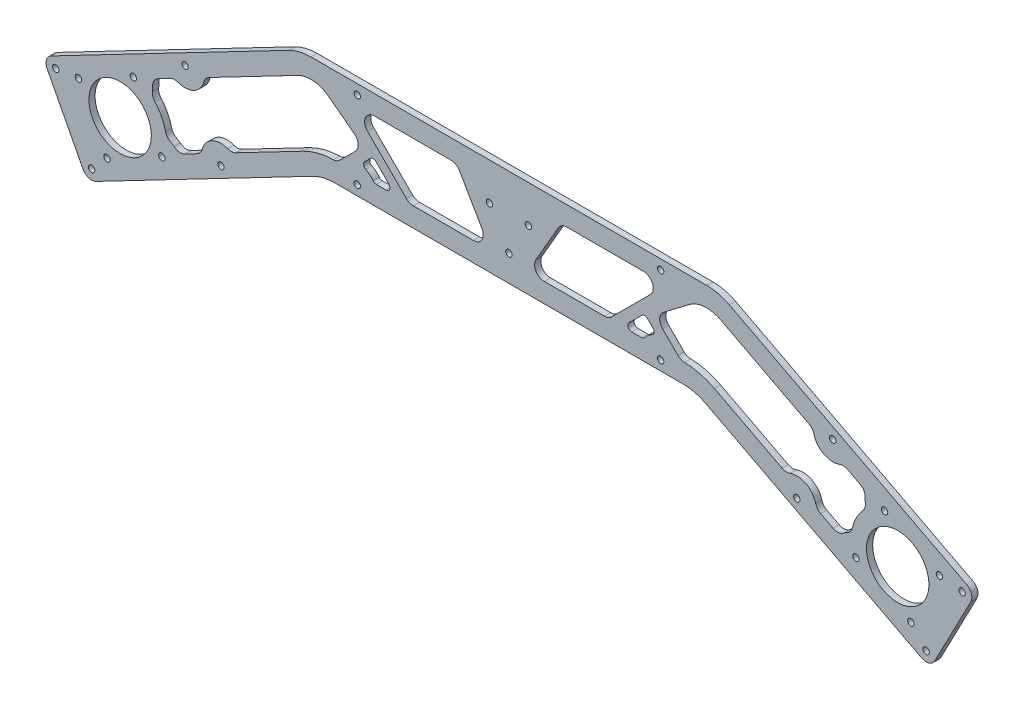
SolidWorks part; units mm, degrees
material "6061-T6 (SS)"
ref_plane "Front Plane" through (0, 0, 0) normal (0, 0, 1) x (1, 0, 0)
ref_plane "Top Plane" through (0, 0, 0) normal (0, 1, 0) x (1, 0, 0)
ref_plane "Right Plane" through (0, 0, 0) normal (1, 0, 0) x (0, 0, -1)
sketch "Sketch1" plane through (0, 0, 0) normal (0, 0, 1) x (1, 0, 0)
  line L0 (-200, -104.1134) -> (0, 0) construction
  line L1 (0, 0) -> (200, -104.1134) construction
  line L2 (-221.4586, -97.3475) -> (-193.2341, -82.6548) construction
  line L3 (-113.3558, -30.8247) -> (-235.4371, -94.3763)
  line L4 (-237.5634, -101.1201) -> (-219.0935, -136.6005)
  line L5 (-212.3497, -138.7268) -> (-101.1208, -80.8247)
  line L6 (-101.8121, -28) -> (101.8121, -28)
  line L7 (0, -28) -> (0, -78) construction
  line L8 (89.5771, -78) -> (-89.5771, -78)
  line L9 (113.3558, -30.8247) -> (235.4371, -94.3763)
  line L10 (237.5634, -101.1201) -> (219.0935, -136.6005)
  line L11 (212.3497, -138.7268) -> (101.1208, -80.8247)
  circle A1 centre (-200, -104.1134) radius 16.05
  circle A2 centre (-221.4586, -97.3475) radius 1.65
  circle A3 centre (-193.2341, -82.6548) radius 1.65
  circle A4 centre (-178.5414, -110.8793) radius 1.65
  circle A5 centre (-206.7659, -125.572) radius 1.65
  arc A6 (-235.4371, -94.3763) -> (-237.5634, -101.1201) centre (-233.1284, -98.8113) ccw
  arc A7 (-219.0935, -136.6005) -> (-212.3497, -138.7268) centre (-214.6584, -134.2918) ccw
  circle A8 centre (0, 0) radius 25 construction
  circle A11 centre (-200, -104.1134) radius 33.55 construction
  circle A12 centre (206.7659, -125.572) radius 1.65
  circle A13 centre (221.4586, -97.3475) radius 1.65
  circle A14 centre (193.2341, -82.6548) radius 1.65
  circle A15 centre (178.5414, -110.8793) radius 1.65
  circle A16 centre (200, -104.1134) radius 16.05
  arc A17 (235.4371, -94.3763) -> (237.5634, -101.1201) centre (233.1284, -98.8113) cw
  arc A18 (219.0935, -136.6005) -> (212.3497, -138.7268) centre (214.6584, -134.2918) cw
  circle A19 centre (-10, -47.2265) radius 1.65
  circle A20 centre (10, -47.2265) radius 1.65
  circle A21 centre (0, -64.547) radius 1.65
  arc A22 (101.1208, -80.8247) -> (89.5771, -78) centre (89.5771, -103) ccw
  arc A23 (113.3558, -30.8247) -> (101.8121, -28) centre (101.8121, -53) ccw
  arc A24 (-113.3558, -30.8247) -> (-101.8121, -28) centre (-101.8121, -53) cw
  arc A25 (-101.1208, -80.8247) -> (-89.5771, -78) centre (-89.5771, -103) cw
  point P17 (-200, -104.1134)
  point P27 (0, -53)
  point P28 (0, -25)
  point P53 (0, -53)
  point P54 (95.6946, -78)
  point P57 (107.9295, -28)
  point P60 (-107.9295, -28)
  point P63 (-95.6946, -78)
  dimension "D1" = 400
  dimension "D3" = 32.1
  dimension "D5" = 3.3
  dimension "D7" = 50
  dimension "D10" = 5
  dimension "D11" = 3.3
  dimension "D12" = 67.1
  dimension "D14" = 3
  dimension "D16" = 25
  dimension "D2" = 125
  dimension "D6" = 45
  dimension "D8" = 3
  dimension "D9" = 50
  dimension "D13" = 50
  dimension "D15" = 20
  dimension "D4" = 4
extrude "Base" add sketch "Sketch1" along normal blind 3.175
sketch "Sketch3" plane through (0, 0, 3.175) normal (0, 0, 1) x (1, 0, 0)
  line L1 (-89.5771, -78) -> (89.5771, -78) construction
  line L2 (-228.3285, -118.8603) -> (-185.7635, -96.7023) construction
  line L3 (101.8121, -28) -> (-101.8121, -28) construction
  line L4 (-237.5634, -101.1201) -> (-219.0935, -136.6005) construction
  line L5 (0, -28) -> (0, -78) construction
  circle A0 centre (-214.6584, -134.2918) radius 1.65
  circle A1 centre (-148.1326, -99.6606) radius 1.65
  circle A2 centre (-78.0312, -73) radius 1.65
  circle A3 centre (-78.0312, -33) radius 1.65
  circle A4 centre (-200, -104.1134) radius 16.05 construction
  circle A5 centre (-166.6026, -64.1802) radius 1.65
  circle A6 centre (-233.1284, -98.8113) radius 1.65
  circle A7 centre (233.1284, -98.8113) radius 1.65
  circle A8 centre (166.6026, -64.1802) radius 1.65
  circle A9 centre (78.0312, -33) radius 1.65
  circle A10 centre (78.0312, -73) radius 1.65
  circle A11 centre (148.1326, -99.6606) radius 1.65
  circle A12 centre (214.6584, -134.2918) radius 1.65
  dimension "D1" = 3.3
  dimension "D3" = 75
  dimension "D6" = 5
  dimension "D4" = 5
  dimension "D5" = 75
  dimension "D2" = 2
extrude "Strut Holes" cut sketch "Sketch3" against normal through all
sketch "Sketch4" plane through (0, 0, 0) normal (0, 0, -1) x (-1, 0, 0)
  line L0 (-166.7326, -103.7062) -> (-160.3585, -100.3881)
  line L1 (-101.1208, -80.8247) -> (-212.3497, -138.7268) construction
  line L2 (-140.5243, -90.063) -> (-105.7383, -71.9546)
  line L3 (-86.9223, -66.5452) -> (-79.0095, -58.6325)
  line L4 (-79.5169, -51.1182) -> (-92.7277, -41.0638)
  line L5 (-180.585, -77.0959) -> (-174.2109, -73.7777)
  line L6 (-235.4371, -94.3763) -> (-113.3558, -30.8247) construction
  line L7 (-154.3768, -63.4527) -> (-108.7383, -39.6948)
  line L8 (89.5771, -78) -> (-89.5771, -78) construction
  line L9 (-68.2844, -68) -> (-63.1994, -68)
  line L10 (-61.7852, -64.5858) -> (-68.4242, -57.9467)
  line L11 (-71.2527, -57.9467) -> (-74.1321, -60.8262)
  line L12 (-25.4306, -40.5) -> (-13.8835, -60.5)
  line L13 (-18.2137, -68) -> (-49.2288, -68)
  line L14 (-52.7643, -66.5355) -> (-72.7643, -46.5355)
  line L15 (-69.2288, -38) -> (-29.7607, -38)
  line L16 (-101.8121, -28) -> (101.8121, -28) construction
  line L17 (0, -28) -> (0, -78) construction
  line L18 (52.7643, -66.5355) -> (72.7643, -46.5355)
  line L19 (18.2137, -68) -> (49.2288, -68)
  line L20 (25.4306, -40.5) -> (13.8835, -60.5)
  line L21 (69.2288, -38) -> (29.7607, -38)
  line L22 (68.2844, -68) -> (63.1994, -68)
  line L23 (61.7852, -64.5858) -> (68.4242, -57.9467)
  line L24 (71.2527, -57.9467) -> (74.1321, -60.8262)
  line L25 (154.3768, -63.4527) -> (108.7383, -39.6948)
  line L26 (180.585, -77.0959) -> (174.2109, -73.7777)
  line L27 (166.7326, -103.7062) -> (160.3585, -100.3881)
  line L28 (140.5243, -90.063) -> (105.7383, -71.9546)
  line L29 (86.9223, -66.5452) -> (79.0095, -58.6325)
  line L30 (79.5169, -51.1182) -> (92.7277, -41.0638)
  arc A0 (-182.112, -88.1128) -> (-176.6329, -98.638) centre (-200, -104.1134) cw
  arc A1 (-174.0237, -101.958) -> (-172.208, -103.1405) centre (-178.5414, -110.8793) cw
  arc A2 (-183.3349, -84.0711) -> (-183.2622, -81.9056) centre (-193.2341, -82.6548) ccw
  arc A3 (-157.8223, -97.1889) -> (-144.5996, -90.3055) centre (-148.1326, -99.6606) cw
  arc A4 (-105.7383, -71.9546) -> (-90.3477, -68.0085) centre (-89.5771, -103) cw
  arc A5 (-89.5771, -78) -> (-101.1208, -80.8247) centre (-89.5771, -103) ccw construction
  arc A6 (-170.1356, -73.5353) -> (-156.9129, -66.6519) centre (-166.6026, -64.1802) ccw
  arc A7 (-108.7383, -39.6948) -> (-92.7277, -41.0638) centre (-101.8121, -53) cw
  arc A8 (-101.8121, -28) -> (-113.3558, -30.8247) centre (-101.8121, -53) ccw construction
  arc A9 (-69.9089, -67.1667) -> (-73.6035, -64.0337) centre (-78.0312, -73) ccw
  circle A10 centre (-10, -47.2265) radius 10 construction
  circle A11 centre (0, -64.547) radius 10 construction
  arc A12 (-156.9129, -66.6519) -> (-154.3768, -63.4527) centre (-152.068, -67.8878) cw
  arc A13 (-174.2109, -73.7777) -> (-170.1356, -73.5353) centre (-171.9022, -78.2128) cw
  arc A14 (-183.2622, -81.9056) -> (-180.585, -77.0959) centre (-178.2763, -81.5309) cw
  arc A15 (-182.112, -88.1128) -> (-183.3349, -84.0711) centre (-178.3853, -84.7793) cw
  arc A16 (-176.6329, -98.638) -> (-174.0237, -101.958) centre (-171.7648, -97.4973) ccw
  arc A17 (-172.208, -103.1405) -> (-166.7326, -103.7062) centre (-169.0413, -99.2712) ccw
  arc A18 (-160.3585, -100.3881) -> (-157.8223, -97.1889) centre (-162.6672, -95.953) ccw
  arc A19 (-144.5996, -90.3055) -> (-140.5243, -90.063) centre (-142.833, -85.628) ccw
  arc A20 (-79.0095, -58.6325) -> (-79.5169, -51.1182) centre (-82.545, -55.0969) ccw
  arc A21 (-90.3477, -68.0085) -> (-86.9223, -66.5452) centre (-90.4578, -63.0097) ccw
  arc A22 (-49.2288, -68) -> (-52.7643, -66.5355) centre (-49.2288, -63) cw
  arc A23 (-25.4306, -40.5) -> (-29.7607, -38) centre (-29.7607, -43) ccw
  arc A24 (-13.8835, -60.5) -> (-18.2137, -68) centre (-18.2137, -63) cw
  arc A25 (-72.7643, -46.5355) -> (-69.2288, -38) centre (-69.2288, -43) cw
  arc A26 (-68.4242, -57.9467) -> (-71.2527, -57.9467) centre (-69.8385, -59.3609) ccw
  arc A27 (-68.2844, -68) -> (-69.9089, -67.1667) centre (-68.2844, -66) cw
  arc A28 (-74.1321, -60.8262) -> (-73.6035, -64.0337) centre (-72.7179, -62.2404) ccw
  arc A29 (-63.1994, -68) -> (-61.7852, -64.5858) centre (-63.1994, -66) ccw
  arc A30 (49.2288, -68) -> (52.7643, -66.5355) centre (49.2288, -63) ccw
  arc A31 (13.8835, -60.5) -> (18.2137, -68) centre (18.2137, -63) ccw
  arc A32 (25.4306, -40.5) -> (29.7607, -38) centre (29.7607, -43) cw
  arc A33 (72.7643, -46.5355) -> (69.2288, -38) centre (69.2288, -43) ccw
  arc A34 (63.1994, -68) -> (61.7852, -64.5858) centre (63.1994, -66) cw
  arc A35 (68.4242, -57.9467) -> (71.2527, -57.9467) centre (69.8385, -59.3609) cw
  arc A36 (68.2844, -68) -> (69.9089, -67.1667) centre (68.2844, -66) ccw
  arc A37 (74.1321, -60.8262) -> (73.6035, -64.0337) centre (72.7179, -62.2404) cw
  arc A38 (69.9089, -67.1667) -> (73.6035, -64.0337) centre (78.0312, -73) cw
  arc A39 (156.9129, -66.6519) -> (154.3768, -63.4527) centre (152.068, -67.8878) ccw
  arc A40 (170.1356, -73.5353) -> (156.9129, -66.6519) centre (166.6026, -64.1802) cw
  arc A41 (174.2109, -73.7777) -> (170.1356, -73.5353) centre (171.9022, -78.2128) ccw
  arc A42 (183.2622, -81.9056) -> (180.585, -77.0959) centre (178.2763, -81.5309) ccw
  arc A43 (183.3349, -84.0711) -> (183.2622, -81.9056) centre (193.2341, -82.6548) cw
  arc A44 (182.112, -88.1128) -> (183.3349, -84.0711) centre (178.3853, -84.7793) ccw
  arc A45 (182.112, -88.1128) -> (176.6329, -98.638) centre (200, -104.1134) ccw
  arc A46 (176.6329, -98.638) -> (174.0237, -101.958) centre (171.7648, -97.4973) cw
  arc A47 (174.0237, -101.958) -> (172.208, -103.1405) centre (178.5414, -110.8793) ccw
  arc A48 (172.208, -103.1405) -> (166.7326, -103.7062) centre (169.0413, -99.2712) cw
  arc A49 (160.3585, -100.3881) -> (157.8223, -97.1889) centre (162.6672, -95.953) cw
  arc A50 (157.8223, -97.1889) -> (144.5996, -90.3055) centre (148.1326, -99.6606) ccw
  arc A51 (144.5996, -90.3055) -> (140.5243, -90.063) centre (142.833, -85.628) cw
  arc A52 (105.7383, -71.9546) -> (90.3477, -68.0085) centre (89.5771, -103) ccw
  arc A53 (90.3477, -68.0085) -> (86.9223, -66.5452) centre (90.4578, -63.0097) cw
  arc A54 (79.0095, -58.6325) -> (79.5169, -51.1182) centre (82.545, -55.0969) cw
  arc A55 (108.7383, -39.6948) -> (92.7277, -41.0638) centre (101.8121, -53) ccw
  point P75 (-74.9619, -54.5849)
  point P78 (-88.3969, -68.0199)
  point P91 (-69.3709, -68)
  point P96 (-58.3709, -68)
  dimension "D1" = 24
  dimension "D2" = 10
  dimension "D4" = 10
  dimension "D5" = 11.5
  dimension "D6" = 5
  dimension "D10" = 2.2457
  dimension "D15" = 5
  dimension "D16" = 5
  dimension "D17" = 2
  dimension "D3" = 10
  dimension "45" = 45
  dimension "D7" = 11.5
  dimension "D8" = 10
  dimension "D9" = 45
  dimension "D11" = 19
  dimension "D12" = 11
  dimension "D13" = 10
  dimension "D14" = 10
extrude "Lightening Holes" cut sketch "Sketch4" against normal through all
